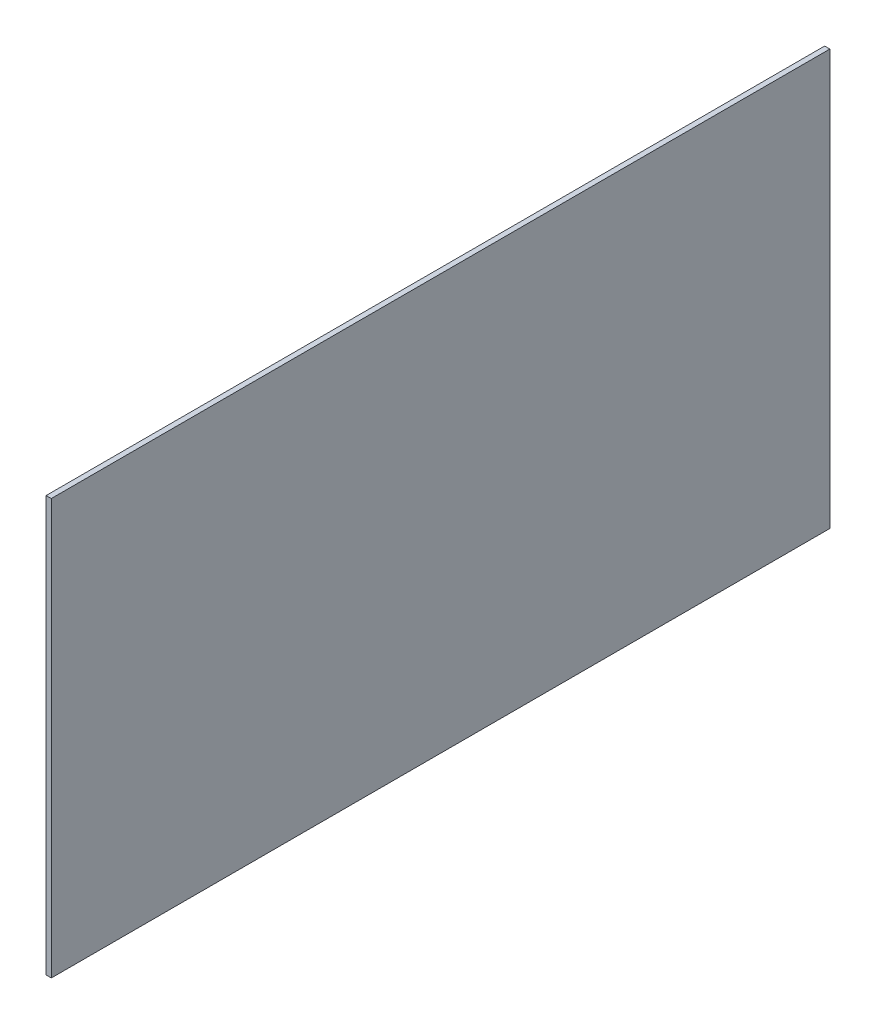
SolidWorks part; units mm, degrees
material "Acrylic (Medium-high impact)"
ref_plane "Front Plane" through (0, 0, 0) normal (0, 0, 1) x (1, 0, 0)
ref_plane "Top Plane" through (0, 0, 0) normal (0, 1, 0) x (1, 0, 0)
ref_plane "Right Plane" through (0, 0, 0) normal (1, 0, 0) x (0, 0, -1)
sketch "Sketch1" plane through (0, 0, 0) normal (1, 0, 0) x (0, 0, -1)
  line L1 (-225, -120) -> (225, -120)
  line L2 (-225, -120) -> (-225, 120)
  line L3 (-225, 120) -> (225, 120)
  line L4 (225, -120) -> (225, 120)
  line L5 (-225, -120) -> (225, 120) construction
  line L6 (-225, 120) -> (225, -120) construction
  point P0 (0, 0)
  dimension "D1" = 450
  dimension "D2" = 240
extrude "Boss-Extrude1" add sketch "Sketch1" along normal mid plane 3
